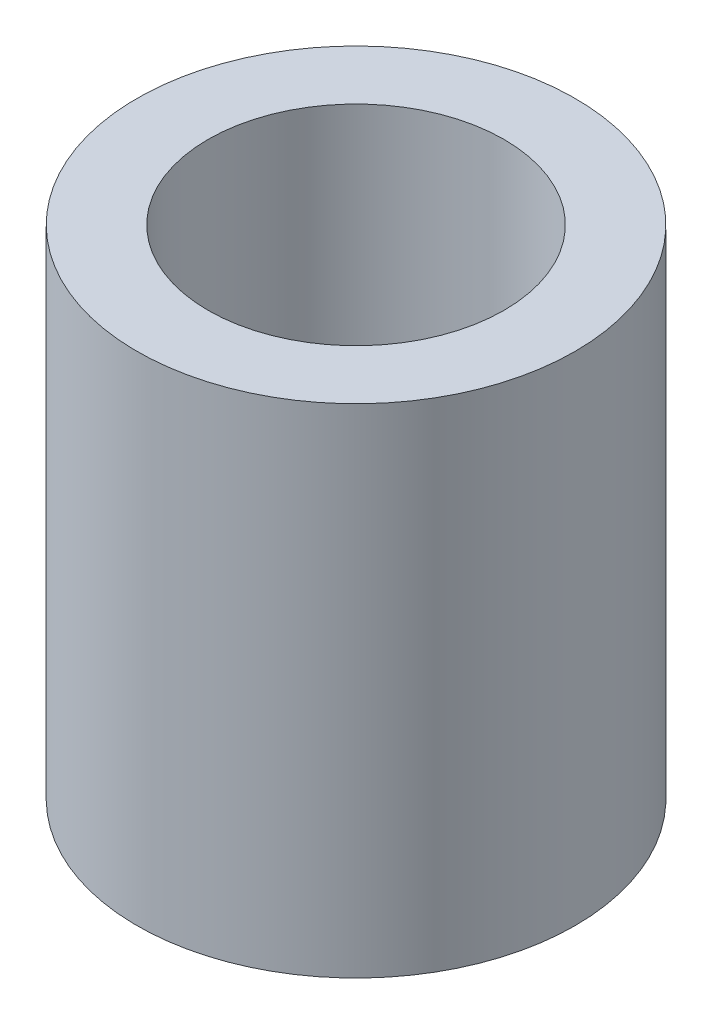
SolidWorks part; units mm, degrees
ref_plane "Plano frontal" through (0, 0, 0) normal (0, 0, 1) x (1, 0, 0)
ref_plane "Plano superior" through (0, 0, 0) normal (0, 1, 0) x (1, 0, 0)
ref_plane "Plano direito" through (0, 0, 0) normal (1, 0, 0) x (0, 0, -1)
sketch "Esboço1" plane through (0, 0, 0) normal (0, 0, 1) x (1, 0, 0)
  line L0 (0, -939.9958) -> (0, 46059.7959) construction
  line L10 (0, 0) -> (-18.5, 0)
  line L11 (0, 0) -> (0, 42)
  line L12 (0, 42) -> (-18.5, 42)
  line L13 (-18.5, 0) -> (-18.5, 42)
  line L18 (-12.5, 42) -> (0, 42)
  line L19 (-12.5, 42) -> (-12.5, 14)
  line L20 (-12.5, 14) -> (0, 14)
  line L21 (0, 42) -> (0, 14)
  dimension "D1" = 42
  dimension "D2" = 18.5
  dimension "D3" = 6
  dimension "D4" = 28
revolve "Revolução1" add sketch "Esboço1" angle 360 about L0
